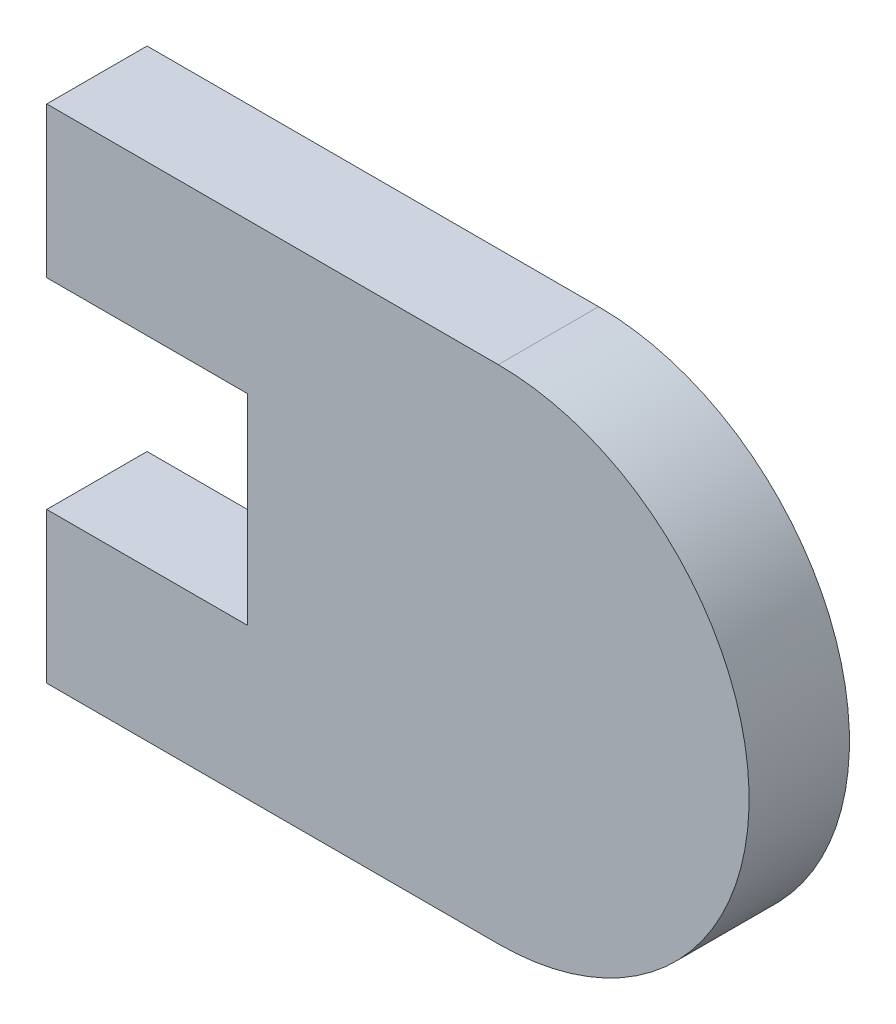
SolidWorks part; units mm, degrees
ref_plane "Front Plane" through (0, 0, 0) normal (0, 0, 1) x (1, 0, 0)
ref_plane "Top Plane" through (0, 0, 0) normal (0, 1, 0) x (1, 0, 0)
ref_plane "Right Plane" through (0, 0, 0) normal (1, 0, 0) x (0, 0, -1)
sketch "Sketch1" plane through (0, 0, 0) normal (0, 0, 1) x (1, 0, 0)
  line L0 (6.35, 7.9375) -> (22.225, 7.9375) construction
  line L1 (0, 0) -> (14.2875, 0)
  line L2 (0, 0) -> (0, 4.7625)
  line L3 (0, 15.875) -> (14.2875, 15.875)
  line L4 (22.225, 0) -> (22.225, 7.9375) construction
  line L5 (0, 11.1125) -> (6.35, 11.1125)
  line L6 (0, 11.1125) -> (0, 4.7625) construction
  line L7 (0, 4.7625) -> (6.35, 4.7625)
  line L8 (6.35, 11.1125) -> (6.35, 4.7625)
  line L9 (22.225, 7.9375) -> (22.225, 15.875) construction
  line L10 (14.2875, 0) -> (22.225, 0) construction
  line L11 (14.2875, 15.875) -> (22.225, 15.875) construction
  line L12 (0, 4.7625) -> (0, 11.1125) construction
  line L13 (0, 11.1125) -> (0, 15.875)
  arc A0 (14.2875, 0) -> (14.2875, 15.875) centre (14.2875, 7.9375) ccw
  arc A1 (6.35, 7.9375) -> (14.2875, 0) centre (14.2875, 7.9375) ccw construction
  arc A2 (14.2875, 15.875) -> (6.35, 7.9375) centre (14.2875, 7.9375) ccw construction
  point P10 (14.2875, 0)
  point P15 (14.2875, 7.9375)
  dimension "D5" = 15.875
  dimension "D1" = 15.875
  dimension "D2" = 6.35
  dimension "D3" = 6.35
  dimension "D4" = 15.875
extrude "Boss-Extrude1" add sketch "Sketch1" along normal blind 3.175
